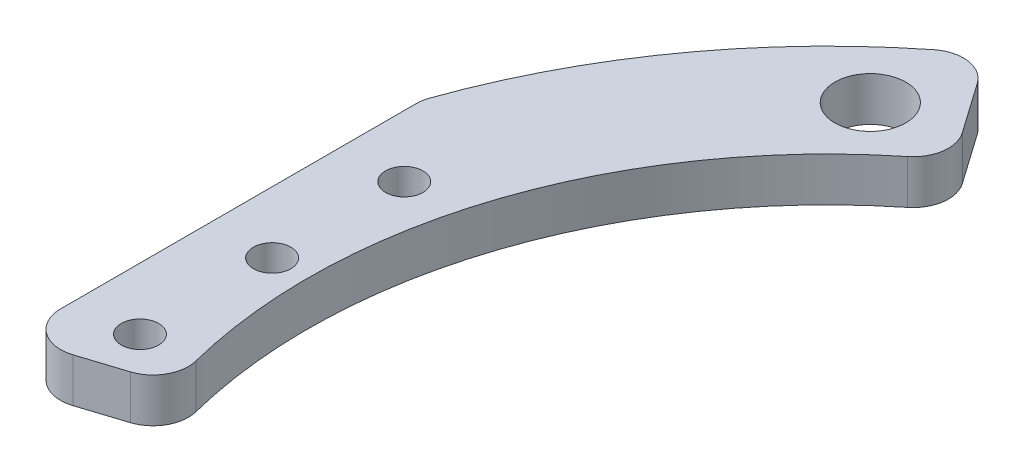
SolidWorks part; units mm, degrees
ref_plane "Front Plane" through (0, 0, 0) normal (0, 0, 1) x (1, 0, 0)
ref_plane "Top Plane" through (0, 0, 0) normal (0, 1, 0) x (1, 0, 0)
ref_plane "Right Plane" through (0, 0, 0) normal (1, 0, 0) x (0, 0, -1)
sketch "Sketch1" plane through (0, 0, 0) normal (0, 1, 0) x (1, 0, 0)
  line L0 (0, 0) -> (-63, 0) construction
  line L1 (-42.5127, 60.5696) -> (-33.8953, 48.2919)
  line L2 (0, 0) -> (-44.3299, 49.2333) construction
  line L15 (-63, -30) -> (-63, 30) construction
  line L16 (-55.5, 0) -> (-70.5, 0) construction
  line L17 (-70.4495, -22.6467) -> (-56.1692, -18.0562)
  circle A0 centre (0, 0) radius 55 construction
  circle A1 centre (0, 0) radius 62.5 construction
  circle A2 centre (-44.3299, 49.2333) radius 3.75 construction
  circle A5 centre (-44.3299, 49.2333) radius 4.025
  circle A7 centre (-63, 0) radius 2.125
  circle A8 centre (-63, -15) radius 2.125
  circle A9 centre (-63, 15) radius 2.125
  arc A10 (-33.8953, 48.2919) -> (-56.1692, -18.0562) centre (0, 0) ccw
  arc A11 (-42.5127, 60.5696) -> (-70.4495, -22.6467) centre (0, 0) ccw
  point P7 (-63, 0)
  dimension "D1" = 110
  dimension "D4" = 125
  dimension "D5" = 7.5
  dimension "D11" = 15
  dimension "D12" = 15
  dimension "D13" = 8.05
  dimension "D8" = 4.25
  dimension "D10" = 5
  dimension "D2" = 59
  dimension "D9" = 15
  dimension "D14" = 8
  dimension "D3" = 63
  dimension "D6" = 66.25
  dimension "D7" = 48
extrude "Boss-Extrude1" add sketch "Sketch1" along normal mid plane 5
sketch "Sketch2" plane through (0, 2.5, 0) normal (0, 1, 0) x (1, 0, 0)
  line L0 (0, 0) -> (-84.4523, 0) construction
  line L2 (-70, 27.6661) -> (-98.9046, 27.6661)
  line L3 (-70, 27.6661) -> (-70, -27.6661)
  line L4 (-70, -27.6661) -> (-98.9046, -27.6661)
  line L5 (-98.9046, 27.6661) -> (-98.9046, -27.6661)
  line L6 (-84.4523, -27.6661) -> (-84.4523, 27.6661) construction
  line L7 (-70, 0) -> (-98.9046, 0) construction
  dimension "D1" = 70
extrude "Cut-Extrude1" cut sketch "Sketch2" against normal through all both and the other way through all
fillet "Fillet1" radius 4 5 edges at (-70, 0, -24) (-70, 0, 22.5022) (-56.1692, 0, 18.0562) (-33.8953, 0, -48.2919) (-42.5127, 0, -60.5696)
